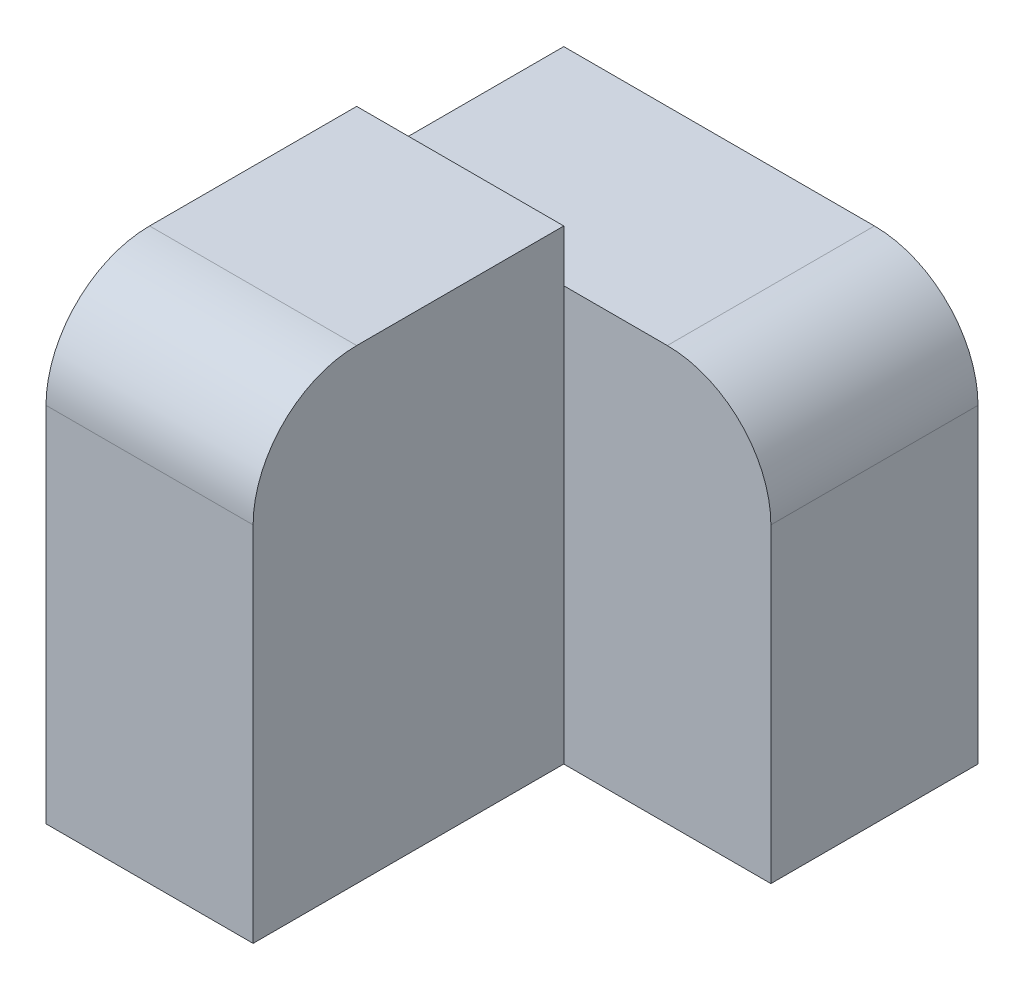
SolidWorks part; units mm, degrees
ref_plane "Front Plane" through (0, 0, 0) normal (0, 0, 1) x (1, 0, 0)
ref_plane "Top Plane" through (0, 0, 0) normal (0, 1, 0) x (1, 0, 0)
ref_plane "Right Plane" through (0, 0, 0) normal (1, 0, 0) x (0, 0, -1)
sketch "Sketch1" plane through (0, 0, 0) normal (0, 0, 1) x (1, 0, 0)
  line L1 (-30, -45) -> (-10, -45)
  line L2 (-10, -45) -> (-10, 0)
  line L3 (-10, 0) -> (-30, 0)
  line L4 (-30, 0) -> (-30, -45)
  dimension "D1" = 20
  dimension "Width" = 45
extrude "Boss-Extrude1" add sketch "Sketch1" along normal blind 30
sketch "Sketch2" plane through (0, 0, 0) normal (0, 0, 1) x (1, 0, 0)
  line L1 (-30, -45) -> (10, -45)
  line L2 (10, -45) -> (10, -5)
  line L3 (10, -5) -> (-30, -5)
  line L4 (-30, -5) -> (-30, -45)
  dimension "D1" = 40
  dimension "Width" = 40
extrude "Boss-Extrude2" add sketch "Sketch2" against normal blind 20
fillet "Fillet1" radius 10 2 edges at (10, -5, -10) (-20, 0, 30)
